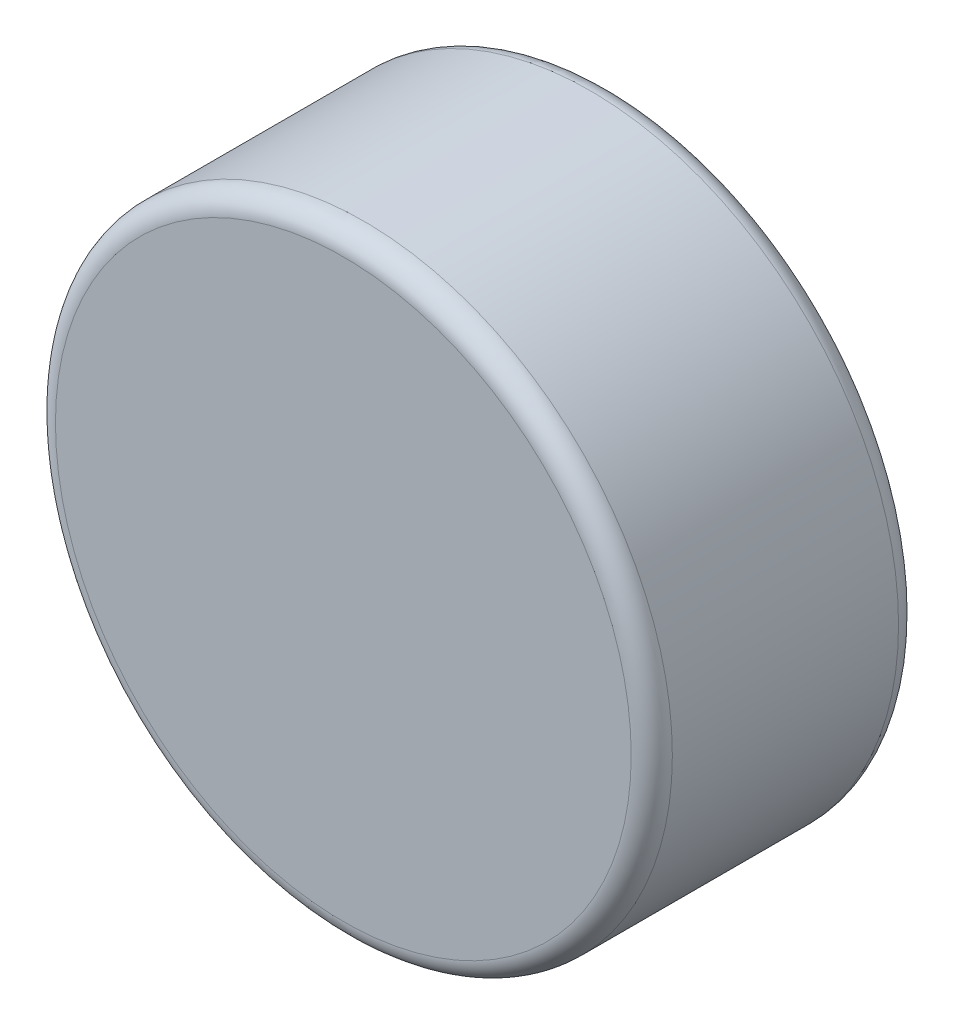
SolidWorks part; units mm, degrees
ref_plane "Plan de face" through (0, 0, 0) normal (0, 0, 1) x (1, 0, 0)
ref_plane "Plan de dessus" through (0, 0, 0) normal (0, 1, 0) x (1, 0, 0)
ref_plane "Plan de droite" through (0, 0, 0) normal (1, 0, 0) x (0, 0, -1)
sketch "Esquisse1" plane through (0, 0, 0) normal (0, 0, 1) x (1, 0, 0)
  circle A0 centre (0, 0) radius 3
extrude "Boss.-Extru.1" add sketch "Esquisse1" along normal blind 2.6
fillet "Congé1" radius 0.2 2 edges at (3, 0, 0) (3, 0, 2.6)
